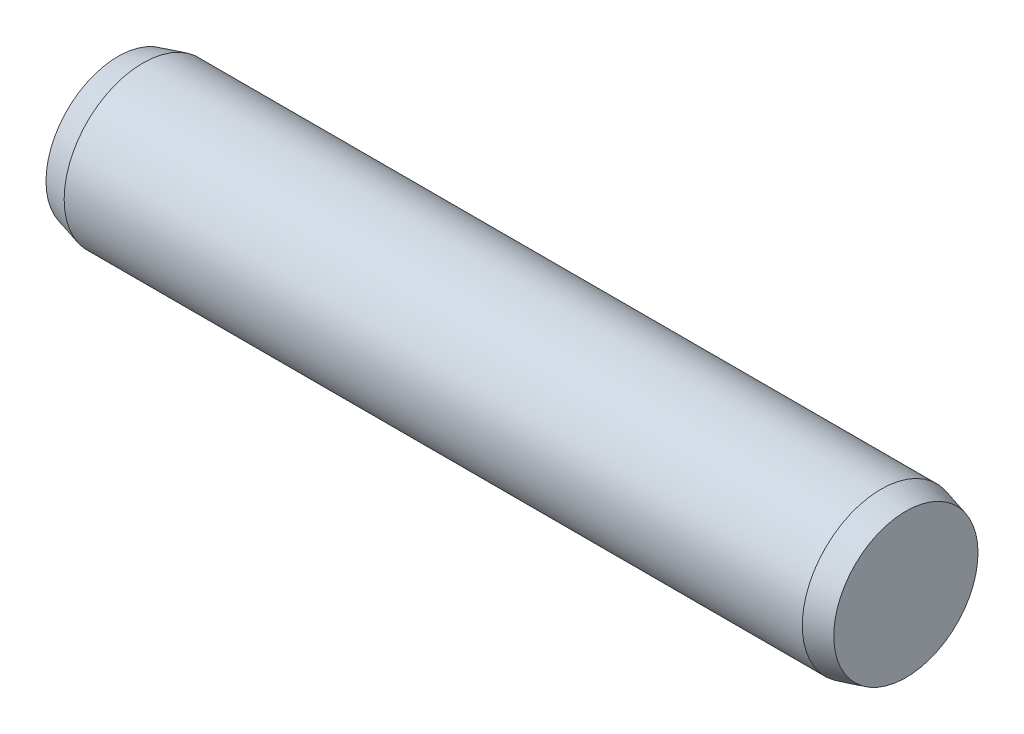
SolidWorks part; units mm, degrees
material "Stainless Steel (ferritic)"
ref_plane "Front Plane" through (0, 0, 0) normal (0, 0, 1) x (1, 0, 0)
ref_plane "Top Plane" through (0, 0, 0) normal (0, 1, 0) x (1, 0, 0)
ref_plane "Right Plane" through (0, 0, 0) normal (1, 0, 0) x (0, 0, -1)
sketch "Sketch1" plane through (0, 0, 0) normal (0, 0, 1) x (1, 0, 0)
  line L0 (-9.37, 0) -> (9.37, 0) construction
  line L1 (9.37, 2) -> (9.37, -2) construction
  line L2 (-9.37, 2) -> (-9.37, -2) construction
  line L3 (10, 2) -> (10, -2) construction
  line L4 (-10, 2) -> (-10, -2) construction
  line L5 (-9.37, 0) -> (-10, 0) construction
  line L6 (9.37, 0) -> (10, 0) construction
  dimension "Dia" = 4
  dimension "C" = 0.63
  dimension "D1" = 0.63
  dimension "Length" = 20
sketch "Sketch2" plane through (0, 0, 0) normal (1, 0, 0) x (0, 0, -1)
  circle A0 centre (0, 0) radius 2
extrude "Extrude1" add sketch "Sketch2" against normal up to vertex (9.37 mm away) and the other way up to vertex (9.37 mm away) up to point (-9.37, 2, 0) other way up to point (9.37, 2, 0)
sketch "Sketch3" plane through (9.37, 0, 0) normal (1, 0, 0) x (0, 0, -1)
  circle A1 centre (0, 0) radius 2
  circle A2 centre (0, 0) radius 2
  dimension "D1" = 0
extrude "Extrude2" add sketch "Sketch3" along normal up to vertex (0.63 mm away) draft 15 up to point (10, 0, 0)
sketch "Sketch4" plane through (-9.37, 0, 0) normal (-1, 0, 0) x (0, 0, 1)
  circle A1 centre (0, 0) radius 2
  circle A2 centre (0, 0) radius 2
  dimension "D1" = 0
extrude "Extrude3" add sketch "Sketch4" along normal up to vertex (0.63 mm away) draft 15 up to point (-10, 0, 0)
equation "\"D1@Sketch1\" = \"C@Sketch1\""
